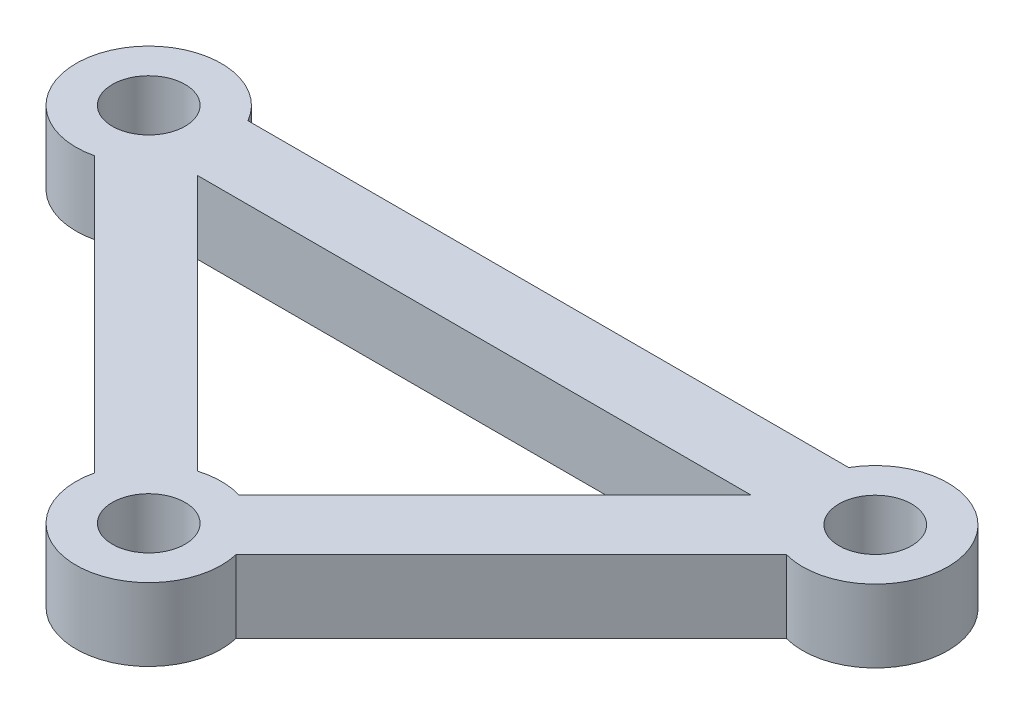
SolidWorks part; units mm, degrees
ref_plane "Front Plane" through (0, 0, 0) normal (0, 0, 1) x (1, 0, 0)
ref_plane "Top Plane" through (0, 0, 0) normal (0, 1, 0) x (1, 0, 0)
ref_plane "Right Plane" through (0, 0, 0) normal (1, 0, 0) x (0, 0, -1)
sketch "Sketch2" plane through (0, 0, 0) normal (0, 1, 0) x (1, 0, 0)
  line L0 (-32.2699, 20.929) -> (9.0699, 20.929)
  line L1 (-30.7447, 15.929) -> (7.3645, 15.929)
  line L3 (12.1059, 13.5994) -> (-6.8241, -5.3306)
  line L4 (13.4, 27.6835) -> (13.4, 8.4106) construction
  line L5 (22.3759, 9.4532) -> (4.7908, 27.0382) construction
  line L6 (-11.6901, -18.8154) -> (-11.6901, 25.4697) construction
  line L7 (-35.4498, 13.5631) -> (-16.5561, -5.3306)
  line L8 (7.3645, 15.929) -> (-10.2554, -1.6908)
  line L9 (-30.7447, 15.929) -> (-13.1248, -1.6908)
  arc A0 (12.1059, 13.5994) -> (9.0699, 20.929) centre (13.4, 18.429) ccw
  circle A1 centre (13.4, 18.429) radius 2.5 construction
  arc A2 (-32.2699, 20.929) -> (-35.4498, 13.5631) centre (-36.6, 18.429) ccw
  circle A3 centre (-36.6, 18.429) radius 2.5 construction
  arc A4 (-10.2554, -1.6908) -> (-13.1248, -1.6908) centre (-11.6901, -6.4805) ccw
  arc A5 (-16.5561, -5.3306) -> (-6.8241, -5.3306) centre (-11.6901, -6.4805) ccw
  point P4 (13.4, 18.429)
  point P5 (-36.6, 18.429)
  point P23 (-11.6901, -6.4805)
  dimension "D4" = 10
  dimension "D5" = 10
  dimension "D11" = 10
  dimension "D1" = 5
  dimension "D6" = 45
  dimension "D10" = 35.3553
extrude "Boss-Extrude1" add sketch "Sketch2" along normal blind 5
hole_wizard "Ø5.0mm Dowel Hole1" positions "Sketch3" profile "Sketch4" hole size "Ø5.0" standard "ANSI Metric" end condition through all
sketch "Sketch3" plane through (0, 5, 0) normal (0, 1, 0) x (1, 0, 0)
  point P0 (13.4, 18.429)
  point P3 (-36.6, 18.429)
  point P6 (-11.6901, -6.4805)
sketch "Sketch4" plane through (13.4, 5, -18.429) normal (1, 0, 0) x (0, 0, 1)
  line L0 (0, 0) -> (0, 5)
  line L1 (0, 5) -> (2.5, 5)
  line L2 (2.5, 5) -> (2.5, 0)
  line L5 (2.5, 0) -> (0, 0)
  line L11 (0, -6.35) -> (0, 107.95) construction
  dimension "Thru Hole Dia." = 5
  dimension "Thru Hole Depth" = 5
equation "\"width\"=5"
equation "\"D1@Sketch2\"=\"width\""
equation "\"D10@Sketch2\"=sqr(2)*25"
